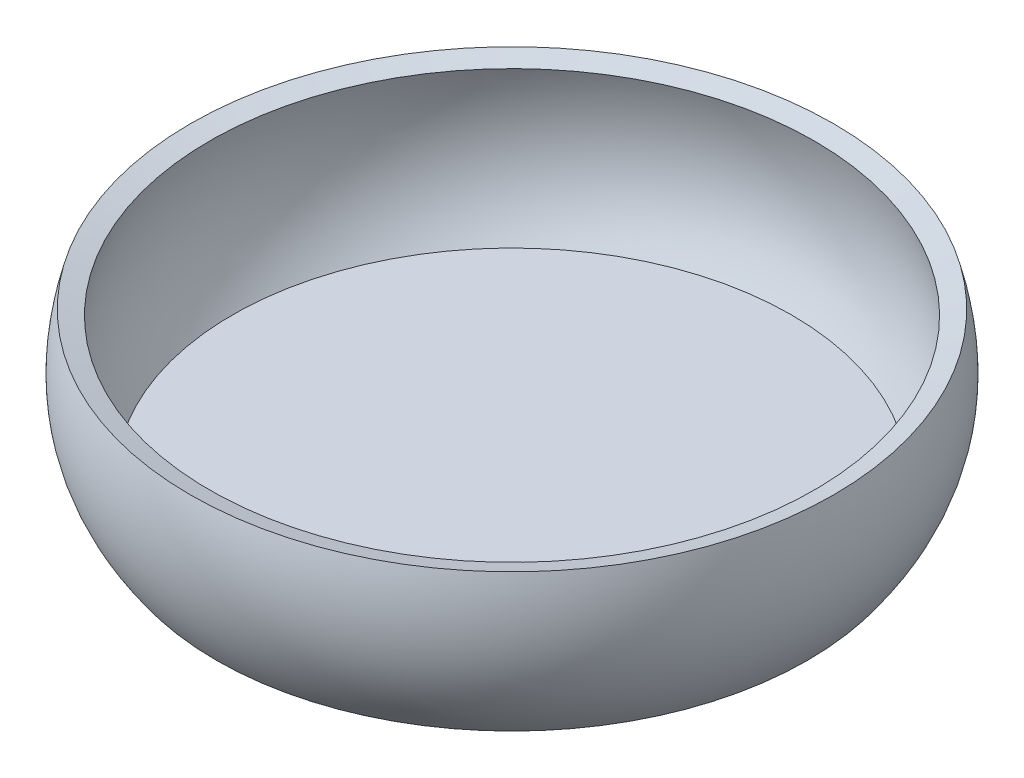
SolidWorks part; units mm, degrees
ref_plane "Front Plane" through (0, 0, 0) normal (0, 0, 1) x (1, 0, 0)
ref_plane "Top Plane" through (0, 0, 0) normal (0, 1, 0) x (1, 0, 0)
ref_plane "Right Plane" through (0, 0, 0) normal (1, 0, 0) x (0, 0, -1)
sketch "Sketch1" plane through (0, 0, 0) normal (0, 0, 1) x (1, 0, 0)
  line L0 (0, 0) -> (50, 0) construction
  line L1 (50, 0) -> (0, 0)
  line L2 (0, 0) -> (50, 0)
  line L3 (47.2835, 2) -> (0, 2)
  line L4 (0, 0) -> (0, 2)
  line L5 (0, 0) -> (0, 20.288) construction
  spline S0 degree 2 poles (50, 0) (58.55, 11.6132) (54.4075, 26.4568) knots 0 0 0 1 1 1
  spline S1 degree 1 poles (47.2835, 2) (51.1583, 25.5501) knots 0 0 1 1 construction
  spline S2 degree 2 poles (47.2835, 2) (50.1534, 5.9141) (52.2213, 12.9245) (52.57, 20.4414) (51.1583, 25.5501) knots 0 0 0 0.375 0.625 1 1 1
  spline S3 degree 1 poles (51.1583, 25.5501) (54.4075, 26.4568) knots 0 0 1 1
  point P7 (47.4978, 1.655)
  point P10 (0, 0)
  dimension "D2" = 27.846
  dimension "D1" = 50
  dimension "D3" = 2
revolve "Revolve1" add sketch "Sketch1" angle 360 about L5
sketch "Sketch2" plane through (0, 0, 0) normal (0, -1, 0) x (1, 0, 0)
  circle A0 centre (25.5965, 20.0268) radius 2.5 construction
  circle A1 centre (17.7206, 13.8647) radius 2.5 construction
  circle A2 centre (25.5965, 20.0268) radius 2.5
  circle A3 centre (17.7206, 13.8647) radius 2.5
extrude "Cut-Extrude2" cut sketch "Sketch2" against normal blind 22
